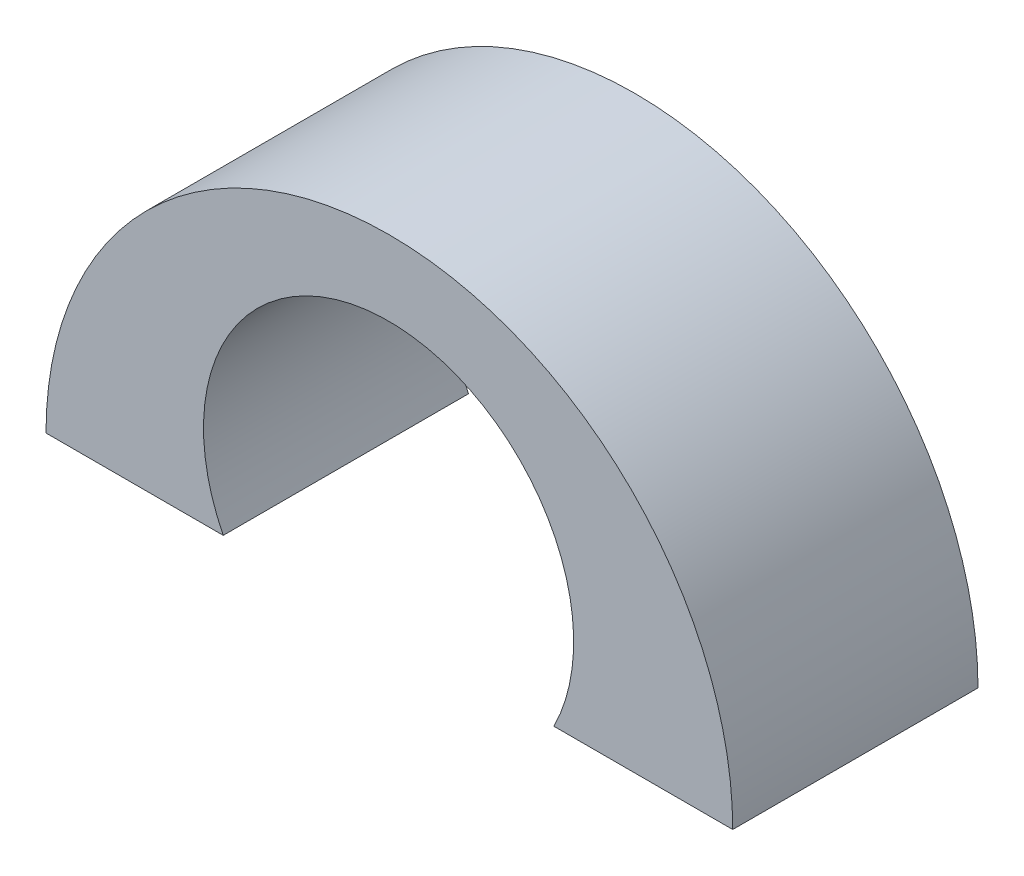
SolidWorks part; units mm, degrees
ref_plane "Plan de face" through (0, 0, 0) normal (0, 0, 1) x (1, 0, 0)
ref_plane "Plan de dessus" through (0, 0, 0) normal (0, 1, 0) x (1, 0, 0)
ref_plane "Plan de droite" through (0, 0, 0) normal (1, 0, 0) x (0, 0, -1)
sketch "Esquisse1" plane through (0, 0, 0) normal (0, 0, 1) x (1, 0, 0)
  line L0 (-3.3865, 0) -> (-7, 0)
  line L1 (3.3545, 0) -> (7, 0)
  arc A0 (-7, 0) -> (7, 0) centre (0, 0) cw
  arc A1 (-3.3865, 0) -> (3.3545, 0) centre (-0.016, 1.6959) cw
  dimension "D1" = 7
  dimension "D2" = 3.6135
  dimension "D3" = 3.6455
extrude "Boss.-Extru.1" add sketch "Esquisse1" along normal blind 5
